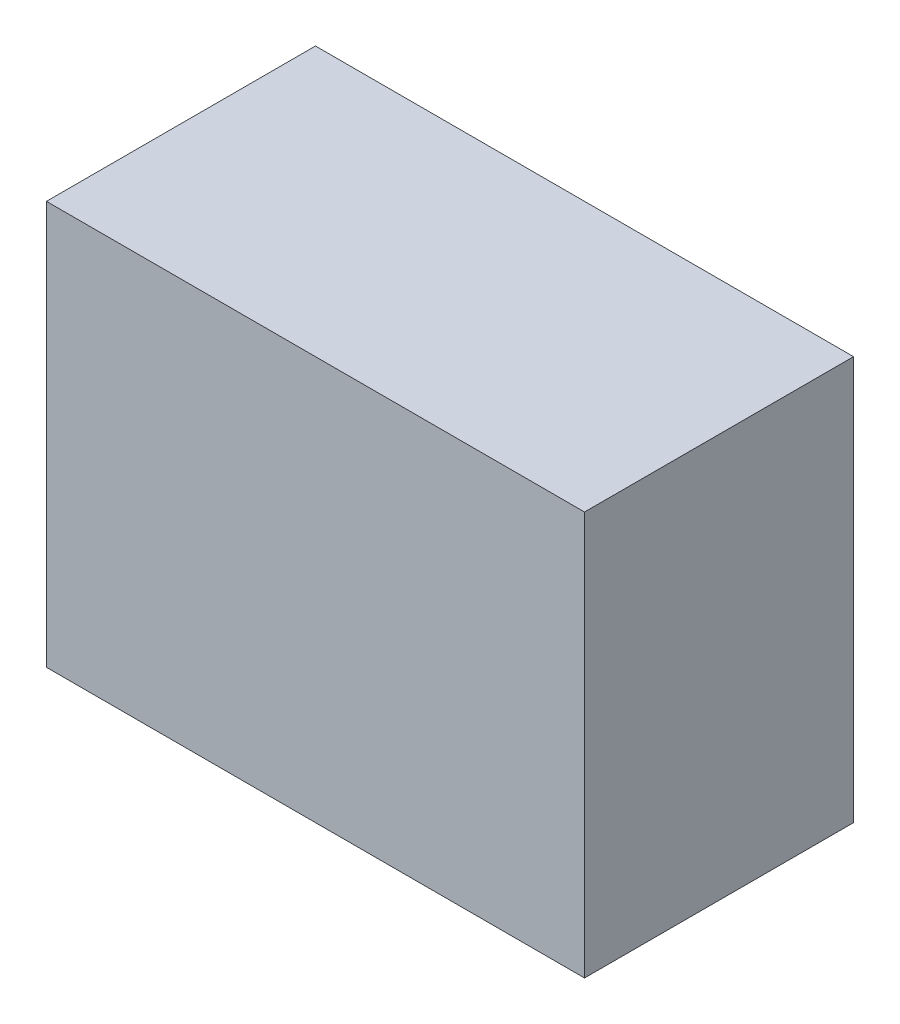
SolidWorks part; units mm, degrees
ref_plane "Front Plane" through (0, 0, 0) normal (0, 0, 1) x (1, 0, 0)
ref_plane "Top Plane" through (0, 0, 0) normal (0, 1, 0) x (1, 0, 0)
ref_plane "Right Plane" through (0, 0, 0) normal (1, 0, 0) x (0, 0, -1)
sketch "Sketch1" plane through (0, 0, 0) normal (0, 0, 1) x (1, 0, 0)
  line L1 (0, 0) -> (40, 0)
  line L2 (0, 0) -> (0, 30)
  line L3 (0, 30) -> (40, 30)
  line L4 (40, 0) -> (40, 30)
  dimension "D1" = 40
  dimension "D2" = 30
extrude "Boss-Extrude1" add sketch "Sketch1" along normal blind 20
sketch "Sketch3" plane through (0, 0, 0) normal (0, 0, -1) x (-1, 0, 0)
  line L0 (-40, 0) -> (-40, 30) construction
  line L1 (0, 0) -> (-40, 0) construction
  circle A0 centre (-20, 15) radius 11
  point P4 (-40, 15)
  dimension "D1" = 22
  dimension "D2" = 20
  dimension "D3" = 15
extrude "Cut-Extrude3" cut sketch "Sketch3" against normal blind 7
